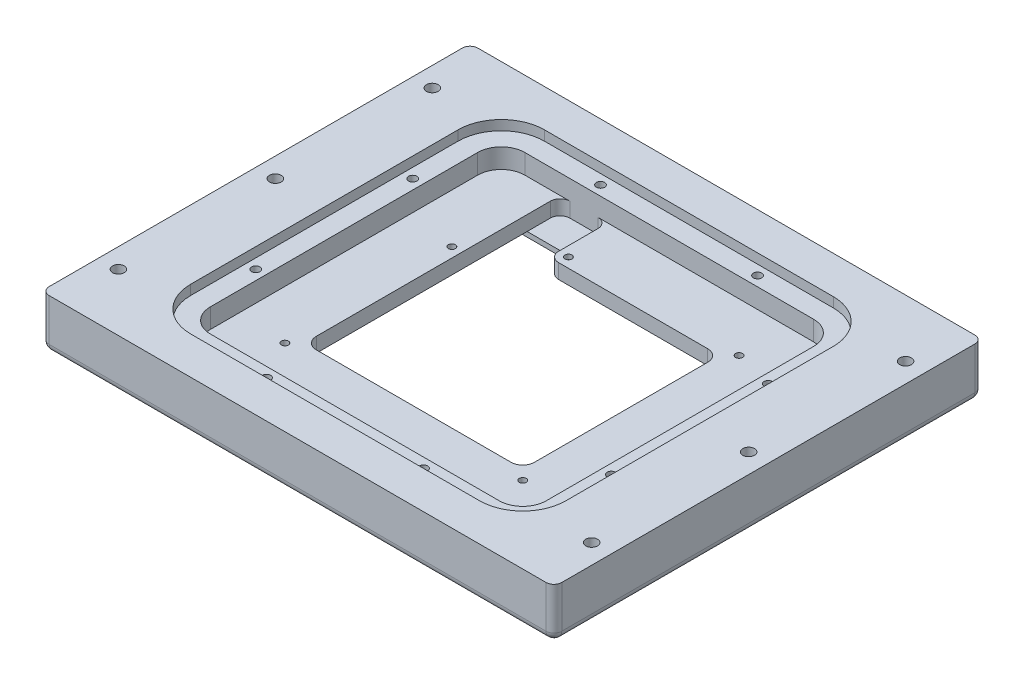
SolidWorks part; units mm, degrees
material "PE High Density"
ref_plane "Front Plane" through (0, 0, 0) normal (0, 0, 1) x (1, 0, 0)
ref_plane "Top Plane" through (0, 0, 0) normal (0, 1, 0) x (1, 0, 0)
ref_plane "Right Plane" through (0, 0, 0) normal (1, 0, 0) x (0, 0, -1)
sketch "Sketch2" plane through (0, 0, 0) normal (0, 1, 0) x (1, 0, 0)
  line L0 (-41.656, 22.1996) -> (-19.9136, 22.1996)
  line L1 (41.656, -38.1762) -> (-41.656, -38.1762)
  line L2 (41.656, -38.1762) -> (41.656, 38.1762)
  line L3 (41.656, 38.1762) -> (-41.656, 38.1762)
  line L4 (-41.656, -38.1762) -> (-41.656, 38.1762)
  line L5 (41.656, -38.1762) -> (-41.656, 38.1762) construction
  line L6 (41.656, 38.1762) -> (-41.656, -38.1762) construction
  line L7 (-19.9136, 22.1996) -> (-19.9136, 38.1762)
  line L8 (73.406, -69.9262) -> (-73.406, -69.9262)
  line L9 (-73.406, -69.9262) -> (-73.406, 69.9262)
  line L10 (73.406, 69.9262) -> (-73.406, 69.9262)
  line L11 (73.406, -69.9262) -> (73.406, 69.9262)
  point P0 (0, 0)
  point P13 (-38.481, -35.0012)
  point P14 (38.481, -35.0012)
  point P15 (38.481, 35.0012)
  point P16 (-16.7386, 35.0012)
  point P17 (-38.481, 19.0246)
  dimension "D1" = 83.312
  dimension "D2" = 76.3524
  dimension "D3" = 21.7424
  dimension "D4" = 15.9766
  dimension "D6" = 3.175
  dimension "D7" = 3.175
  dimension "D8" = 57.2008
  dimension "D9" = 80.137
  dimension "D10" = 24.9174
  dimension "D11" = 73.1774
  dimension "D5" = 31.75
extrude "Boss-Extrude1" add sketch "Sketch2" along normal blind 15.875 contours L8 L11 L10 L9 L1 L4 L3 L2 | L0 L7 L3 L4
sketch "Sketch4" plane through (0, 0, 0) normal (0, 1, 0) x (1, 0, 0)
  line L0 (41.656, -38.1762) -> (41.656, 38.1762) construction
  line L1 (41.656, 38.1762) -> (-19.9136, 38.1762) construction
  line L2 (41.656, -38.1762) -> (-41.656, -38.1762) construction
  line L3 (-41.656, -38.1762) -> (-41.656, 22.1996) construction
  line L4 (-41.656, 22.1996) -> (-19.9136, 22.1996) construction
  line L5 (41.656, -38.1762) -> (41.656, 38.1762)
  line L6 (41.656, 38.1762) -> (-19.9136, 38.1762)
  line L7 (41.656, -38.1762) -> (-41.656, -38.1762)
  line L8 (-41.656, -38.1762) -> (-41.656, 22.1996)
  line L9 (-41.656, 22.1996) -> (-19.9136, 22.1996)
  line L10 (-19.9136, 22.1996) -> (-19.9136, 38.1762) construction
  line L11 (-19.9136, 22.1996) -> (-19.9136, 38.1762)
  line L12 (35.306, 31.8262) -> (-13.5636, 31.8262)
  line L13 (-13.5636, 15.8496) -> (-13.5636, 31.8262)
  line L14 (-35.306, 15.8496) -> (-13.5636, 15.8496)
  line L15 (-35.306, -31.8262) -> (-35.306, 15.8496)
  line L16 (35.306, -31.8262) -> (-35.306, -31.8262)
  line L17 (35.306, -31.8262) -> (35.306, 31.8262)
  dimension "D1" = 6.35
extrude "Boss-Extrude2" add sketch "Sketch4" along normal blind 9.525
sketch "Sketch5" plane through (0, 0, 0) normal (0, -1, 0) x (1, 0, 0)
  line L5 (46.736, -50.8762) -> (-46.736, -50.8762)
  line L6 (54.356, -43.2562) -> (54.356, 43.2562)
  line L7 (46.736, 50.8762) -> (-46.736, 50.8762)
  line L8 (-54.356, -43.2562) -> (-54.356, 43.2562)
  line L9 (54.356, -50.8762) -> (-54.356, 50.8762) construction
  line L10 (54.356, 50.8762) -> (-54.356, -50.8762) construction
  arc A0 (46.736, -50.8762) -> (54.356, -43.2562) centre (46.736, -43.2562) ccw
  arc A1 (-46.736, -50.8762) -> (-54.356, -43.2562) centre (-46.736, -43.2562) cw
  arc A2 (54.356, 43.2562) -> (46.736, 50.8762) centre (46.736, 43.2562) ccw
  arc A3 (-46.736, 50.8762) -> (-54.356, 43.2562) centre (-46.736, 43.2562) ccw
  point P0 (0, 0)
  dimension "D3" = 7.62
  dimension "D1" = 108.712
  dimension "D2" = 101.7524
extrude "Cut-Extrude2" cut sketch "Sketch5" against normal blind 3.175
hole_wizard "M2.5x0.45 Tapped Hole1" positions "Sketch6" profile "Sketch7" tap size "M2.5x0.45" standard "ANSI Metric"
sketch "Sketch6" plane through (0, 3.175, 0) normal (0, -1, 0) x (-1, 0, 0)
  point P0 (38.481, -35.0012)
  point P3 (-38.481, -35.0012)
  point P6 (38.481, 19.0246)
  point P9 (16.7386, 35.0012)
  point P12 (-38.481, 35.0012)
sketch "Sketch7" plane through (-38.481, 3.175, 35.0012) normal (1, 0, 0) x (0, 0, -1)
  line L0 (0, 0) -> (0, 6.9659)
  line L1 (0, 6.9659) -> (1.025, 6.35)
  line L2 (1.025, 6.35) -> (1.025, 0)
  line L5 (1.025, 0) -> (0, 0)
  line L10 (0, 6.9659) -> (-1.025, 6.35) construction
  line L11 (0, -6.35) -> (0, 107.95) construction
  dimension "Tap Drill Dia." = 2.05
  dimension "Tap Drill Depth" = 6.35
  dimension "Drill Angle" = 118
cosmetic thread "Hole Thread1" parameters "D1"=5.08, "D2"=2.5
cosmetic thread "Hole Thread2" parameters "D1"=5.08, "D2"=2.5
cosmetic thread "Hole Thread3" parameters "D1"=5.08, "D2"=2.5
cosmetic thread "Hole Thread4" parameters "D1"=5.08, "D2"=2.5
cosmetic thread "Hole Thread5" parameters "D1"=5.08, "D2"=2.5
sketch "Sketch10" plane through (0, 15.875, 0) normal (0, 1, 0) x (1, 0, 0)
  line L4 (54.356, -43.2562) -> (54.356, 43.2562)
  line L5 (-46.736, -50.8762) -> (46.736, -50.8762)
  line L6 (-54.356, 43.2562) -> (-54.356, -43.2562)
  line L7 (46.736, 50.8762) -> (-46.736, 50.8762)
  line L8 (54.356, -43.2562) -> (54.356, 43.2562)
  line L9 (-46.736, -50.8762) -> (46.736, -50.8762)
  line L10 (-54.356, 43.2562) -> (-54.356, -43.2562)
  line L11 (46.736, 50.8762) -> (-46.736, 50.8762)
  arc A4 (54.356, 43.2562) -> (46.736, 50.8762) centre (46.736, 43.2562) ccw
  arc A5 (46.736, -50.8762) -> (54.356, -43.2562) centre (46.736, -43.2562) ccw
  arc A6 (-54.356, -43.2562) -> (-46.736, -50.8762) centre (-46.736, -43.2562) ccw
  arc A7 (-46.736, 50.8762) -> (-54.356, 43.2562) centre (-46.736, 43.2562) ccw
  arc A8 (54.356, 43.2562) -> (46.736, 50.8762) centre (46.736, 43.2562) ccw
  arc A9 (46.736, -50.8762) -> (54.356, -43.2562) centre (46.736, -43.2562) ccw
  arc A10 (-54.356, -43.2562) -> (-46.736, -50.8762) centre (-46.736, -43.2562) ccw
  arc A11 (-46.736, 50.8762) -> (-54.356, 43.2562) centre (-46.736, 43.2562) ccw
  dimension "D1" = 0
extrude "Cut-Extrude3" cut sketch "Sketch10" against normal up to surface (6.35 mm away) up to face at (-38.481, 9.525, 33.9762)
sketch "Sketch11" plane through (0, 3.175, 0) normal (0, -1, 0) x (1, 0, 0)
  line L8 (43.688, 40.2082) -> (-43.688, 40.2082)
  line L9 (-43.688, 40.2082) -> (-43.688, -40.2082)
  line L10 (-43.688, -40.2082) -> (43.688, -40.2082)
  line L11 (43.688, -40.2082) -> (43.688, 40.2082)
  line L12 (40.513, 40.2082) -> (-40.513, 40.2082)
  line L13 (-43.688, 37.0332) -> (-43.688, -37.0332)
  line L14 (-40.513, -40.2082) -> (40.513, -40.2082)
  line L15 (43.688, -37.0332) -> (43.688, 37.0332)
  arc A0 (40.513, -40.2082) -> (43.688, -37.0332) centre (40.513, -37.0332) ccw
  arc A1 (-43.688, -37.0332) -> (-40.513, -40.2082) centre (-40.513, -37.0332) ccw
  arc A2 (40.513, 40.2082) -> (43.688, 37.0332) centre (40.513, 37.0332) cw
  arc A3 (-40.513, 40.2082) -> (-43.688, 37.0332) centre (-40.513, 37.0332) ccw
  dimension "D2" = 3.175
  dimension "D1" = 2.032
extrude "Cut-Extrude4" cut sketch "Sketch11" against normal blind 1.6
sketch "Sketch12" plane through (0, 4.775, 0) normal (0, -1, 0) x (1, 0, 0)
  line L0 (-35.306, 31.8262) -> (-35.306, -15.8496) construction
  line L1 (35.306, 31.8262) -> (-35.306, 31.8262)
  line L2 (35.306, 31.8262) -> (35.306, -31.8262)
  line L3 (35.306, -31.8262) -> (-35.306, -31.8262)
  line L4 (-35.306, 31.8262) -> (-35.306, -31.8262)
  line L5 (-13.5636, -31.8262) -> (35.306, -31.8262) construction
extrude "Cut-Extrude5" cut sketch "Sketch12" against normal through all
fillet "Fillet1" radius 3.81 4 edges at (35.306, 7.15, -31.8262) (-35.306, 7.15, -31.8262) (35.306, 7.15, 31.8262) (-35.306, 7.15, 31.8262)
sketch "Sketch13" plane through (0, 0, 0) normal (0, -1, 0) x (1, 0, 0)
  line L4 (54.356, -43.2562) -> (54.356, 43.2562)
  line L5 (46.736, 50.8762) -> (-46.736, 50.8762)
  line L6 (-54.356, 43.2562) -> (-54.356, -43.2562)
  line L7 (-46.736, -50.8762) -> (46.736, -50.8762)
  line L8 (54.356, -43.2562) -> (54.356, 43.2562)
  line L9 (46.736, 50.8762) -> (-46.736, 50.8762)
  line L10 (-54.356, 43.2562) -> (-54.356, -43.2562)
  line L11 (-46.736, -50.8762) -> (46.736, -50.8762)
  line L12 (73.406, 69.9262) -> (-73.406, 69.9262)
  line L13 (-73.406, 69.9262) -> (-73.406, -69.9262)
  line L14 (-73.406, -69.9262) -> (73.406, -69.9262)
  line L15 (73.406, -69.9262) -> (73.406, 69.9262)
  line L16 (73.406, 69.9262) -> (-73.406, 69.9262)
  line L17 (-73.406, 69.9262) -> (-73.406, -69.9262)
  line L18 (-73.406, -69.9262) -> (73.406, -69.9262)
  line L19 (73.406, -69.9262) -> (73.406, 69.9262)
  arc A4 (46.736, -50.8762) -> (54.356, -43.2562) centre (46.736, -43.2562) ccw
  arc A5 (54.356, 43.2562) -> (46.736, 50.8762) centre (46.736, 43.2562) ccw
  arc A6 (-46.736, 50.8762) -> (-54.356, 43.2562) centre (-46.736, 43.2562) ccw
  arc A7 (-54.356, -43.2562) -> (-46.736, -50.8762) centre (-46.736, -43.2562) ccw
  arc A8 (46.736, -50.8762) -> (54.356, -43.2562) centre (46.736, -43.2562) ccw
  arc A9 (54.356, 43.2562) -> (46.736, 50.8762) centre (46.736, 43.2562) ccw
  arc A10 (-46.736, 50.8762) -> (-54.356, 43.2562) centre (-46.736, 43.2562) ccw
  arc A11 (-54.356, -43.2562) -> (-46.736, -50.8762) centre (-46.736, -43.2562) ccw
  dimension "D1" = 0
  dimension "D2" = 0
extrude "Cut-Extrude6" cut sketch "Sketch13" against normal blind 1.5875
fillet "Fillet2" [suppressed] radius 1.5875
sketch "Sketch14" plane through (0, 9.525, 0) normal (0, 1, 0) x (1, 0, 0)
  line L1 (-35.306, 28.0162) -> (-19.9136, 28.0162)
  line L2 (-35.306, 28.0162) -> (-35.306, 50.8762)
  line L3 (-35.306, 50.8762) -> (-19.9136, 50.8762)
  line L4 (-19.9136, 28.0162) -> (-19.9136, 50.8762)
  line L6 (46.736, 50.8762) -> (-46.736, 50.8762) construction
  circle A0 centre (-16.7386, 35.0012) radius 1.025 construction
  dimension "D1" = 3.175
extrude "Cut-Extrude7" cut sketch "Sketch14" against normal up to surface (4.75 mm away) up to face at (0, 4.775, 0)
fillet "Fillet3" radius 3.175 3 edges at (-19.9136, 7.15, -50.8762) (-35.306, 7.15, -50.8762) (-19.9136, 7.15, -31.8262)
sketch "Sketch15" plane through (0, 15.875, 0) normal (0, 1, 0) x (1, 0, 0)
  line L0 (54.356, -43.2562) -> (54.356, 43.2562) construction
  line L1 (-46.736, -50.8762) -> (46.736, -50.8762) construction
  line L2 (-54.356, 43.2562) -> (-54.356, -43.2562) construction
  line L3 (46.736, 50.8762) -> (-46.736, 50.8762) construction
  line L4 (54.356, -43.2562) -> (54.356, 43.2562)
  line L5 (-46.736, -50.8762) -> (46.736, -50.8762)
  line L6 (-54.356, 43.2562) -> (-54.356, -43.2562)
  line L7 (46.736, 50.8762) -> (-46.736, 50.8762)
  line L8 (60.706, -43.2562) -> (60.706, 43.2562)
  line L9 (46.736, 57.2262) -> (-46.736, 57.2262)
  line L10 (-60.706, 43.2562) -> (-60.706, -43.2562)
  line L11 (-46.736, -57.2262) -> (46.736, -57.2262)
  line L16 (-73.406, -69.9262) -> (73.406, -69.9262)
  line L17 (73.406, -69.9262) -> (73.406, 69.9262)
  line L18 (73.406, 69.9262) -> (-73.406, 69.9262)
  line L19 (-73.406, 69.9262) -> (-73.406, -69.9262)
  line L20 (-73.406, -69.9262) -> (73.406, -69.9262)
  line L21 (73.406, -69.9262) -> (73.406, 69.9262)
  line L22 (73.406, 69.9262) -> (-73.406, 69.9262)
  line L23 (-73.406, 69.9262) -> (-73.406, -69.9262)
  arc A0 (46.736, -50.8762) -> (54.356, -43.2562) centre (46.736, -43.2562) ccw construction
  arc A1 (-54.356, -43.2562) -> (-46.736, -50.8762) centre (-46.736, -43.2562) ccw construction
  arc A2 (54.356, 43.2562) -> (46.736, 50.8762) centre (46.736, 43.2562) ccw construction
  arc A3 (-46.736, 50.8762) -> (-54.356, 43.2562) centre (-46.736, 43.2562) ccw construction
  arc A4 (46.736, -50.8762) -> (54.356, -43.2562) centre (46.736, -43.2562) ccw
  arc A5 (-54.356, -43.2562) -> (-46.736, -50.8762) centre (-46.736, -43.2562) ccw
  arc A6 (54.356, 43.2562) -> (46.736, 50.8762) centre (46.736, 43.2562) ccw
  arc A7 (-46.736, 50.8762) -> (-54.356, 43.2562) centre (-46.736, 43.2562) ccw
  arc A8 (60.706, 43.2562) -> (46.736, 57.2262) centre (46.736, 43.2562) ccw
  arc A9 (-46.736, 57.2262) -> (-60.706, 43.2562) centre (-46.736, 43.2562) ccw
  arc A10 (-60.706, -43.2562) -> (-46.736, -57.2262) centre (-46.736, -43.2562) ccw
  arc A11 (46.736, -57.2262) -> (60.706, -43.2562) centre (46.736, -43.2562) ccw
  line M29 (-73.406, -69.9262) -> (73.406, -69.9262)
  line M30 (73.406, -69.9262) -> (73.406, 69.9262)
  line M31 (73.406, 69.9262) -> (-73.406, 69.9262)
  line M32 (-73.406, 69.9262) -> (-73.406, -69.9262)
  dimension "D1" = 6.35
  dimension "D2" = 0
extrude "Boss-Extrude3" add sketch "Sketch15" along normal blind 3.175 contours A11 L11 A10 L10 A9 L9 A8 L8 M32 M29 M30 M31
hole_wizard "#6-32 Tapped Hole1" positions "Sketch16" profile "Sketch18" tap size "#6-32" standard "ANSI Inch"
sketch "Sketch16" plane through (0, 15.875, 0) normal (0, 1, 0) x (1, 0, 0)
  line L28 (57.531, -43.2562) -> (57.531, 43.2562)
  line L29 (-46.736, -54.0512) -> (46.736, -54.0512)
  line L30 (-57.531, 43.2562) -> (-57.531, -43.2562)
  line L31 (46.736, 54.0512) -> (-46.736, 54.0512)
  line L32 (57.531, -43.2562) -> (57.531, 43.2562) construction
  line L33 (-46.736, -54.0512) -> (46.736, -54.0512) construction
  line L34 (-57.531, 43.2562) -> (-57.531, -43.2562) construction
  line L35 (46.736, 54.0512) -> (-46.736, 54.0512) construction
  arc A24 (57.531, 43.2562) -> (46.736, 54.0512) centre (46.736, 43.2562) ccw
  arc A25 (46.736, -54.0512) -> (57.531, -43.2562) centre (46.736, -43.2562) ccw
  arc A26 (-57.531, -43.2562) -> (-46.736, -54.0512) centre (-46.736, -43.2562) ccw
  arc A27 (-46.736, 54.0512) -> (-57.531, 43.2562) centre (-46.736, 43.2562) ccw
  arc A28 (57.531, 43.2562) -> (46.736, 54.0512) centre (46.736, 43.2562) ccw construction
  arc A29 (46.736, -54.0512) -> (57.531, -43.2562) centre (46.736, -43.2562) ccw construction
  arc A30 (-57.531, -43.2562) -> (-46.736, -54.0512) centre (-46.736, -43.2562) ccw construction
  arc A31 (-46.736, 54.0512) -> (-57.531, 43.2562) centre (-46.736, 43.2562) ccw construction
  point P141 (-25.4, 54.0512)
  point P143 (-57.531, 25.4)
  point P145 (-57.531, -25.4)
  point P147 (-25.4, -54.0512)
  dimension "D2" = 25.4
  dimension "D3" = 25.4
  dimension "D4" = 25.4
  dimension "D1" = 3.175
cosmetic thread "Hole Thread6" parameters "D1"=14.224, "D2"=3.5052
cosmetic thread "Hole Thread7" parameters "D1"=14.224, "D2"=3.5052
cosmetic thread "Hole Thread8" parameters "D1"=14.224, "D2"=3.5052
cosmetic thread "Hole Thread9" parameters "D1"=14.224, "D2"=3.5052
sketch "Sketch18" plane through (-25.4, 15.875, 54.0512) normal (1, 0, 0) x (0, 0, 1)
  line L0 (0, 0) -> (0, 10.3377)
  line L1 (0, 10.3377) -> (1.3525, 9.525)
  line L2 (1.3525, 9.525) -> (1.3525, 0)
  line L5 (1.3525, 0) -> (0, 0)
  line L10 (0, 10.3377) -> (-1.3526, 9.525) construction
  line L11 (0, -6.35) -> (0, 107.95) construction
  dimension "Tap Drill Dia." = 2.7051
  dimension "Tap Drill Depth" = 9.525
  dimension "Drill Angle" = 118
mirror "Mirror1" about plane through (0, 0, 0) normal (1, 0, 0) of "#6-32 Tapped Hole1"
cosmetic thread "Hole Thread10" parameters "D1"=14.224, "D2"=3.5052
cosmetic thread "Hole Thread11" parameters "D1"=14.224, "D2"=3.5052
cosmetic thread "Hole Thread12" parameters "D1"=14.224, "D2"=3.5052
cosmetic thread "Hole Thread13" parameters "D1"=14.224, "D2"=3.5052
sketch "Sketch19" plane through (0, 4.775, 0) normal (0, -1, 0) x (1, 0, 0)
  circle A0 centre (38.481, 35.0012) radius 2.7813
  circle A1 centre (38.481, -35.0012) radius 2.7813
  circle A2 centre (-38.481, 35.0012) radius 2.7813
  circle A3 centre (-38.481, -19.0246) radius 2.7813
  circle A4 centre (-16.7386, -35.0012) radius 2.7813
  point P0 (38.481, 35.0012)
  dimension "D1" = 5.5626
  dimension "D2" = 5.5626
  dimension "D3" = 5.5626
  dimension "D4" = 5.5626
  dimension "D5" = 5.5626
extrude "Cut-Extrude8" cut sketch "Sketch19" against normal blind 3.175
hole_wizard "#4-40 Tapped Hole1" positions "Sketch20" profile "Sketch21" tap size "#4-40" standard "ANSI Inch"
sketch "Sketch20" plane through (0, 9.525, 0) normal (0, 1, 0) x (1, 0, 0)
  point P0 (-38.481, 19.0246)
  point P3 (-16.7386, 35.0012)
  point P6 (38.481, 35.0012)
  point P9 (38.481, -35.0012)
  point P12 (-38.481, -35.0012)
sketch "Sketch21" plane through (-38.481, 9.525, -19.0246) normal (1, 0, 0) x (0, 0, 1)
  line L0 (0, 0) -> (0, 8.2992)
  line L1 (0, 8.2992) -> (1.1303, 7.62)
  line L2 (1.1303, 7.62) -> (1.1303, 0)
  line L5 (1.1303, 0) -> (0, 0)
  line L10 (0, 8.2992) -> (-1.1303, 7.62) construction
  line L11 (0, -6.35) -> (0, 107.95) construction
  dimension "Tap Drill Dia." = 2.2606
  dimension "Tap Drill Depth" = 7.62
  dimension "Drill Angle" = 118
cosmetic thread "Hole Thread14" parameters "D1"=5.588, "D2"=2.8448
cosmetic thread "Hole Thread15" parameters "D1"=5.588, "D2"=2.8448
cosmetic thread "Hole Thread16" parameters "D1"=5.588, "D2"=2.8448
cosmetic thread "Hole Thread17" parameters "D1"=5.588, "D2"=2.8448
cosmetic thread "Hole Thread18" parameters "D1"=5.588, "D2"=2.8448
sketch "Sketch22" plane through (0, 1.5875, 0) normal (0, -1, 0) x (1, 0, 0)
  line L0 (73.406, -69.9262) -> (73.406, 69.9262) construction
  line L1 (73.406, 69.9262) -> (-73.406, 69.9262)
  line L2 (73.406, 69.9262) -> (73.406, -69.9262)
  line L3 (73.406, -69.9262) -> (-73.406, -69.9262)
  line L4 (-73.406, 69.9262) -> (-73.406, -69.9262)
  line L5 (73.406, 69.9262) -> (-73.406, 69.9262) construction
  line L6 (-73.406, 69.9262) -> (-73.406, -69.9262) construction
  line L7 (-73.406, -69.9262) -> (73.406, -69.9262) construction
extrude "Cut-Extrude9" cut sketch "Sketch22" against normal blind 1.524
sketch "Sketch23" plane through (0, 3.175, 0) normal (0, -1, 0) x (1, 0, 0)
  line L9 (46.736, 44.2722) -> (-46.736, 44.2722)
  line L10 (46.736, 44.2722) -> (46.736, 50.8762)
  line L11 (46.736, 50.8762) -> (-46.736, 50.8762)
  line L12 (-46.736, 44.2722) -> (-46.736, 50.8762)
  line L13 (54.356, 43.2562) -> (47.752, 43.2562)
  line L14 (54.356, 43.2562) -> (54.356, -43.2562)
  line L15 (54.356, -43.2562) -> (47.752, -43.2562)
  line L16 (47.752, 43.2562) -> (47.752, -43.2562)
  line L17 (46.736, -50.8762) -> (-46.736, -50.8762)
  line L18 (46.736, -50.8762) -> (46.736, -44.2722)
  line L19 (46.736, -44.2722) -> (-46.736, -44.2722)
  line L20 (-46.736, -50.8762) -> (-46.736, -44.2722)
  line L21 (-54.356, 43.2562) -> (-47.752, 43.2562)
  line L22 (-54.356, 43.2562) -> (-54.356, -43.2562)
  line L23 (-54.356, -43.2562) -> (-47.752, -43.2562)
  line L24 (-47.752, 43.2562) -> (-47.752, -43.2562)
  arc A0 (54.356, -43.2562) -> (46.736, -50.8762) centre (46.736, -43.2562) cw
  arc A1 (47.752, -43.2562) -> (46.736, -44.2722) centre (46.736, -43.2562) cw
  arc A2 (-46.736, -50.8762) -> (-54.356, -43.2562) centre (-46.736, -43.2562) cw
  arc A3 (-46.736, -44.2722) -> (-47.752, -43.2562) centre (-46.736, -43.2562) cw
  arc A4 (-54.356, 43.2562) -> (-46.736, 50.8762) centre (-46.736, 43.2562) cw
  arc A5 (-47.752, 43.2562) -> (-46.736, 44.2722) centre (-46.736, 43.2562) cw
  arc A6 (46.736, 50.8762) -> (54.356, 43.2562) centre (46.736, 43.2562) cw
  arc A7 (46.736, 44.2722) -> (47.752, 43.167) centre (46.6914, 43.2116) cw
  arc M26 (46.736, -50.8762) -> (54.356, -43.2562) centre (46.736, -43.2562) ccw
  line M27 (54.356, -43.2562) -> (54.356, 43.2562)
  arc M28 (54.356, 43.2562) -> (46.736, 50.8762) centre (46.736, 43.2562) ccw
  line M29 (46.736, 50.8762) -> (-46.736, 50.8762)
  arc M30 (-46.736, 50.8762) -> (-54.356, 43.2562) centre (-46.736, 43.2562) ccw
  line M31 (-54.356, 43.2562) -> (-54.356, -43.2562)
  arc M32 (-54.356, -43.2562) -> (-46.736, -50.8762) centre (-46.736, -43.2562) ccw
  line M33 (-46.736, -50.8762) -> (46.736, -50.8762)
  dimension "D1" = 6.604
extrude "Cut-Extrude10" cut sketch "Sketch23" against normal blind 0.6801 contours L21 A5 L12 M30 | L12 L9 L10 M29 | L24 L21 L23 M31 | L10 A7 L13 M28 | L13 A7 L16 L15 M27 | L15 A1 L18 M26 | L20 L18 L19 M33 | L20 A3 L23 M32
sketch "Sketch24" plane through (0, 19.05, 0) normal (0, 1, 0) x (1, 0, 0)
  line L0 (-73.406, -69.9262) -> (73.406, -69.9262) construction
  line L1 (73.406, -69.9262) -> (73.406, 69.9262) construction
  line L2 (-73.406, 69.9262) -> (-73.406, -69.9262) construction
  line L3 (73.406, 69.9262) -> (-73.406, 69.9262) construction
  point P0 (67.056, -69.9262)
  point P1 (73.406, 63.5762)
  point P4 (67.056, 69.9262)
  point P5 (-67.056, -69.9262)
  point P6 (73.406, -63.5762)
  point P7 (-73.406, 63.5762)
  point P10 (-73.406, -63.5762)
  point P17 (-67.056, 69.9262)
  point P18 (-67.056, -63.5762)
  point P21 (-67.056, 63.5762)
  point P22 (67.056, -63.5762)
  point P23 (67.056, 63.5762)
  dimension "D1" = 6.35
  dimension "D2" = 6.35
  dimension "D3" = 6.35
  dimension "D4" = 6.35
  dimension "D5" = 6.35
  dimension "D6" = 6.35
  dimension "D7" = 6.35
  dimension "D8" = 6.35
hole_wizard "1/4-20 Tapped Hole1" [suppressed] positions "Sketch27" profile "Sketch28" tap size "1/4-20" standard "ANSI Inch"
sketch "Sketch27" plane through (0, 19.05, 0) normal (0, 1, 0) x (1, 0, 0)
  point P0 (67.056, -63.5762)
  point P9 (67.056, 63.5762)
  point P24 (41.656, -63.5762)
  point P26 (67.056, -38.1762)
  point P28 (67.056, 38.1762)
  point P30 (41.656, 63.5762)
  point P39 (16.256, -63.5762)
  point P41 (67.056, -12.7762)
  point P43 (67.056, 12.7762)
  point P45 (16.256, 63.5762)
  dimension "D1" = 25.4
  dimension "D2" = 25.4
  dimension "D3" = 25.4
  dimension "D4" = 25.4
  dimension "D5" = 25.4
  dimension "D6" = 25.4
sketch "Sketch28" plane through (67.056, 19.05, 63.5762) normal (1, 0, 0) x (0, 0, 1)
  line L0 (0, 0) -> (0, 18.0438)
  line L1 (0, 18.0438) -> (2.5527, 16.51)
  line L2 (2.5527, 16.51) -> (2.5527, 0)
  line L5 (2.5527, 0) -> (0, 0)
  line L10 (0, 18.0438) -> (-2.5527, 16.51) construction
  line L11 (0, -6.35) -> (0, 107.95) construction
  dimension "Tap Drill Dia." = 5.1054
  dimension "Tap Drill Depth" = 16.51
  dimension "Drill Angle" = 118
cosmetic thread "Hole Thread19" [suppressed] parameters "D1"=12.7, "D2"=6.35
cosmetic thread "Hole Thread20" [suppressed] parameters "D1"=12.7, "D2"=6.35
cosmetic thread "Hole Thread21" [suppressed] parameters "D1"=12.7, "D2"=6.35
cosmetic thread "Hole Thread22" [suppressed] parameters "D1"=12.7, "D2"=6.35
cosmetic thread "Hole Thread23" [suppressed] parameters "D1"=12.7, "D2"=6.35
cosmetic thread "Hole Thread24" [suppressed] parameters "D1"=12.7, "D2"=6.35
cosmetic thread "Hole Thread25" [suppressed] parameters "D1"=12.7, "D2"=6.35
cosmetic thread "Hole Thread26" [suppressed] parameters "D1"=12.7, "D2"=6.35
cosmetic thread "Hole Thread27" [suppressed] parameters "D1"=12.7, "D2"=6.35
cosmetic thread "Hole Thread28" [suppressed] parameters "D1"=12.7, "D2"=6.35
mirror "Mirror2" [suppressed] about plane through (0, 0, 0) normal (1, 0, 0)
cosmetic thread "Hole Thread29" [suppressed] parameters "D1"=12.7, "D2"=6.35
cosmetic thread "Hole Thread30" [suppressed] parameters "D1"=12.7, "D2"=6.35
cosmetic thread "Hole Thread31" [suppressed] parameters "D1"=12.7, "D2"=6.35
cosmetic thread "Hole Thread32" [suppressed] parameters "D1"=12.7, "D2"=6.35
cosmetic thread "Hole Thread33" [suppressed] parameters "D1"=12.7, "D2"=6.35
cosmetic thread "Hole Thread34" [suppressed] parameters "D1"=12.7, "D2"=6.35
cosmetic thread "Hole Thread35" [suppressed] parameters "D1"=12.7, "D2"=6.35
cosmetic thread "Hole Thread36" [suppressed] parameters "D1"=12.7, "D2"=6.35
cosmetic thread "Hole Thread37" [suppressed] parameters "D1"=12.7, "D2"=6.35
cosmetic thread "Hole Thread38" [suppressed] parameters "D1"=12.7, "D2"=6.35
sketch "Sketch29" plane through (0, 19.05, 0) normal (0, 1, 0) x (1, 0, 0)
  line L0 (-82.931, 79.4512) -> (-82.931, -79.4512)
  line L1 (-82.931, -79.4512) -> (82.931, -79.4512)
  line L2 (82.931, -79.4512) -> (82.931, 79.4512)
  line L3 (82.931, 79.4512) -> (-82.931, 79.4512)
  line L4 (-73.406, 69.9262) -> (-73.406, -69.9262)
  line L5 (-73.406, -69.9262) -> (73.406, -69.9262)
  line L6 (73.406, -69.9262) -> (73.406, 69.9262)
  line L7 (73.406, 69.9262) -> (-73.406, 69.9262)
  line L8 (-73.406, 69.9262) -> (-73.406, -69.9262)
  line L9 (-73.406, -69.9262) -> (73.406, -69.9262)
  line L10 (73.406, -69.9262) -> (73.406, 69.9262)
  line L11 (73.406, 69.9262) -> (-73.406, 69.9262)
  dimension "D1" = 0
  dimension "D2" = 9.525
extrude "Boss-Extrude4" add sketch "Sketch29" against normal up to surface (15.9385 mm away) up to face at (0, 3.1115, 0)
sketch "Sketch30" plane through (0, 3.1115, 0) normal (0, -1, 0) x (1, 0, 0)
  line L0 (46.736, 50.8762) -> (-46.736, 50.8762) construction
  line L1 (46.736, 50.8762) -> (-46.736, 50.8762)
  line L2 (-54.356, 43.2562) -> (-54.356, -43.2562) construction
  line L3 (-54.356, 43.2562) -> (-54.356, -43.2562)
  line L4 (-82.931, -79.4512) -> (82.931, -79.4512)
  line L5 (82.931, -79.4512) -> (82.931, 79.4512)
  line L6 (82.931, 79.4512) -> (-82.931, 79.4512)
  line L7 (-82.931, 79.4512) -> (-82.931, -79.4512)
  line L8 (-82.931, -79.4512) -> (82.931, -79.4512)
  line L9 (82.931, -79.4512) -> (82.931, 79.4512)
  line L10 (82.931, 79.4512) -> (-82.931, 79.4512)
  line L11 (-82.931, 79.4512) -> (-82.931, -79.4512)
  line L14 (-46.736, -50.8762) -> (46.736, -50.8762)
  line L15 (-54.356, 43.2562) -> (-54.356, -43.2562)
  line L16 (46.736, 50.8762) -> (-46.736, 50.8762)
  line L17 (54.356, -43.2562) -> (54.356, 43.2562)
  line L18 (-46.736, -50.8762) -> (46.736, -50.8762)
  line L19 (-54.356, 43.2562) -> (-54.356, -43.2562)
  line L20 (46.736, 50.8762) -> (-46.736, 50.8762)
  line L21 (54.356, -43.2562) -> (54.356, 43.2562)
  arc A0 (-46.736, 50.8762) -> (-54.356, 43.2562) centre (-46.736, 43.2562) ccw construction
  arc A1 (-46.736, 50.8762) -> (-54.356, 43.2562) centre (-46.736, 43.2562) ccw
  arc A4 (-54.356, -43.2562) -> (-46.736, -50.8762) centre (-46.736, -43.2562) ccw
  arc A5 (-46.736, 50.8762) -> (-54.356, 43.2562) centre (-46.736, 43.2562) ccw
  arc A6 (54.356, 43.2562) -> (46.736, 50.8762) centre (46.736, 43.2562) ccw
  arc A7 (46.736, -50.8762) -> (54.356, -43.2562) centre (46.736, -43.2562) ccw
  arc A8 (-54.356, -43.2562) -> (-46.736, -50.8762) centre (-46.736, -43.2562) ccw
  arc A9 (-46.736, 50.8762) -> (-54.356, 43.2562) centre (-46.736, 43.2562) ccw
  arc A10 (54.356, 43.2562) -> (46.736, 50.8762) centre (46.736, 43.2562) ccw
  arc A11 (46.736, -50.8762) -> (54.356, -43.2562) centre (46.736, -43.2562) ccw
  dimension "D1" = 0
  dimension "D2" = 0
extrude "Boss-Extrude5" add sketch "Sketch30" along normal blind 0.2718
sketch "Sketch31" [suppressed] plane through (0, 19.05, 0) normal (0, 1, 0) x (1, 0, 0)
  circle A0 centre (16.256, -63.5762) radius 2.5527 construction
  circle A1 centre (67.056, -12.7762) radius 2.5527 construction
  circle A2 centre (67.056, 12.7762) radius 2.5527 construction
  circle A3 centre (16.256, 63.5762) radius 2.5527 construction
  circle A4 centre (-16.256, 63.5762) radius 2.5527 construction
  circle A5 centre (-67.056, 12.7762) radius 2.5527 construction
  circle A6 centre (-67.056, -12.7762) radius 2.5527 construction
  circle A7 centre (-16.256, -63.5762) radius 2.5527 construction
  circle A8 centre (16.256, -63.5762) radius 2.5527
  circle A9 centre (67.056, -12.7762) radius 2.5527
  circle A10 centre (67.056, 12.7762) radius 2.5527
  circle A11 centre (16.256, 63.5762) radius 2.5527
  circle A12 centre (-16.256, 63.5762) radius 2.5527
  circle A13 centre (-67.056, 12.7762) radius 2.5527
  circle A14 centre (-67.056, -12.7762) radius 2.5527
  circle A15 centre (-16.256, -63.5762) radius 2.5527
extrude "Boss-Extrude6" [suppressed] add sketch "Sketch31" against normal up to surface (16.2103 mm away)
sketch "Sketch32" [suppressed] plane through (0, 19.05, 0) normal (0, 1, 0) x (1, 0, 0)
  line L0 (82.931, -79.4512) -> (82.931, 79.4512) construction
  line L1 (-82.931, -79.4512) -> (82.931, -79.4512) construction
  line L2 (-82.931, 79.4512) -> (-82.931, -79.4512) construction
  line L3 (82.931, 79.4512) -> (-82.931, 79.4512) construction
  line L4 (82.931, -79.4512) -> (82.931, 79.4512)
  line L5 (-82.931, -79.4512) -> (82.931, -79.4512)
  line L6 (-82.931, 79.4512) -> (-82.931, -79.4512)
  line L7 (82.931, 79.4512) -> (-82.931, 79.4512)
  line L9 (76.581, -73.1012) -> (-76.581, -73.1012)
  line L10 (76.581, -73.1012) -> (76.581, 73.1012)
  line L11 (76.581, 73.1012) -> (-76.581, 73.1012)
  line L12 (-76.581, -73.1012) -> (-76.581, 73.1012)
  line L13 (76.581, -73.1012) -> (-76.581, 73.1012) construction
  line L14 (76.581, 73.1012) -> (-76.581, -73.1012) construction
  circle A0 centre (-67.056, 63.5762) radius 2.5527 construction
  point P3 (0, 0)
  dimension "D1" = 9.525
  dimension "D2" = 9.525
extrude "Cut-Extrude11" [suppressed] cut sketch "Sketch32" against normal through all
sketch "Sketch33" [suppressed] plane through (0, 19.05, 0) normal (0, 1, 0) x (1, 0, 0)
  line L0 (76.581, 73.1012) -> (-76.581, 73.1012) construction
  line L1 (83.185, -73.1012) -> (-83.185, -73.1012)
  line L2 (83.185, -73.1012) -> (83.185, 73.1012)
  line L3 (83.185, 73.1012) -> (-83.185, 73.1012)
  line L4 (-83.185, -73.1012) -> (-83.185, 73.1012)
  line L5 (83.185, -73.1012) -> (-83.185, 73.1012) construction
  line L6 (83.185, 73.1012) -> (-83.185, -73.1012) construction
  line L7 (-76.581, 73.1012) -> (-76.581, -73.1012) construction
  line L12 (-46.736, -57.2262) -> (46.736, -57.2262)
  line L13 (-60.706, 43.2562) -> (-60.706, -43.2562)
  line L14 (46.736, 57.2262) -> (-46.736, 57.2262)
  line L15 (60.706, -43.2562) -> (60.706, 43.2562)
  line L16 (-46.736, -57.2262) -> (46.736, -57.2262)
  line L17 (-60.706, 43.2562) -> (-60.706, -43.2562)
  line L18 (46.736, 57.2262) -> (-46.736, 57.2262)
  line L19 (60.706, -43.2562) -> (60.706, 43.2562)
  arc A0 (-46.736, 57.2262) -> (-60.706, 43.2562) centre (-46.736, 43.2562) ccw construction
  arc A1 (-46.736, 57.2262) -> (-60.706, 43.2562) centre (-46.736, 43.2562) ccw
  arc A4 (46.736, -57.2262) -> (60.706, -43.2562) centre (46.736, -43.2562) ccw
  arc A5 (-60.706, -43.2562) -> (-46.736, -57.2262) centre (-46.736, -43.2562) ccw
  arc A6 (-46.736, 57.2262) -> (-60.706, 43.2562) centre (-46.736, 43.2562) ccw
  arc A7 (60.706, 43.2562) -> (46.736, 57.2262) centre (46.736, 43.2562) ccw
  arc A8 (46.736, -57.2262) -> (60.706, -43.2562) centre (46.736, -43.2562) ccw
  arc A9 (-60.706, -43.2562) -> (-46.736, -57.2262) centre (-46.736, -43.2562) ccw
  arc A10 (-46.736, 57.2262) -> (-60.706, 43.2562) centre (-46.736, 43.2562) ccw
  arc A11 (60.706, 43.2562) -> (46.736, 57.2262) centre (46.736, 43.2562) ccw
  point P0 (0, 0)
  arc M13 (60.706, -43.2562) -> (46.736, -57.2262) centre (46.736, -43.2562) cw
  line M14 (46.736, -57.2262) -> (-46.736, -57.2262)
  arc M15 (-46.736, -57.2262) -> (-60.706, -43.2562) centre (-46.736, -43.2562) cw
  line M16 (-60.706, -43.2562) -> (-60.706, 43.2562)
  arc M17 (-60.706, 43.2562) -> (-46.736, 57.2262) centre (-46.736, 43.2562) cw
  line M18 (-46.736, 57.2262) -> (46.736, 57.2262)
  arc M19 (46.736, 57.2262) -> (60.706, 43.2562) centre (46.736, 43.2562) cw
  line M20 (60.706, 43.2562) -> (60.706, -43.2562)
  circle M21 centre (41.656, 63.5762) radius 2.5527
  circle M22 centre (67.056, 38.1762) radius 2.5527
  circle M23 centre (67.056, -38.1762) radius 2.5527
  circle M24 centre (41.656, -63.5762) radius 2.5527
  circle M25 centre (67.056, 63.5762) radius 2.5527
  circle M26 centre (67.056, -63.5762) radius 2.5527
  circle M27 centre (-41.656, 63.5762) radius 2.5527
  circle M28 centre (-67.056, 38.1762) radius 2.5527
  circle M29 centre (-67.056, -38.1762) radius 2.5527
  circle M30 centre (-41.656, -63.5762) radius 2.5527
  circle M31 centre (-67.056, 63.5762) radius 2.5527
  circle M32 centre (-67.056, -63.5762) radius 2.5527
  line M33 (76.581, 73.1012) -> (-76.581, 73.1012)
  line M34 (-76.581, 73.1012) -> (-76.581, -73.1012)
  line M35 (-76.581, -73.1012) -> (76.581, -73.1012)
  line M36 (76.581, -73.1012) -> (76.581, 73.1012)
  dimension "D1" = 6.604
  dimension "D2" = 0
extrude "Boss-Extrude7" [suppressed] add sketch "Sketch33" against normal up to surface (16.2103 mm away) contours M36 M33 M34 M35 M22 M24 M26 M28 M30 M32 M31 M29 M27 M25 M23 M21 M20 M13 M14 M15 M16 M17 M18 M19 | L4 L1 L3 M34 | L2 L3 L1 M36
sketch "Sketch34" plane through (0, 19.05, 0) normal (0, 1, 0) x (1, 0, 0)
  line L0 (82.931, -79.4512) -> (82.931, 79.4512) construction
  line L1 (-82.931, -79.4512) -> (82.931, -79.4512)
  line L2 (-82.931, -79.4512) -> (-82.931, -69.3649)
  line L3 (-82.931, -69.3649) -> (82.931, -69.3649)
  line L4 (82.931, -79.4512) -> (82.931, -69.3649)
  line L5 (-82.931, 79.4512) -> (-82.931, -79.4512) construction
  line L6 (82.931, 79.4512) -> (-82.931, 79.4512)
  line L7 (82.931, 79.4512) -> (82.931, 69.3649)
  line L8 (82.931, 69.3649) -> (-82.931, 69.3649)
  line L9 (-82.931, 79.4512) -> (-82.931, 69.3649)
  dimension "D1" = 10.0863
  dimension "D2" = 10.0863
extrude "Cut-Extrude12" cut sketch "Sketch34" against normal through all
fillet "Fillet4" radius 2.54 8 edges at (-82.931, 2.8397, 0) (82.931, 2.8397, 0) (0, 2.8397, 69.3649) (0, 2.8397, -69.3649) (-82.931, 10.9449, -69.3649) (82.931, 10.9449, -69.3649) (-82.931, 10.9449, 69.3649) (82.931, 10.9449, 69.3649)
hole_wizard "CBORE for #6 Socket Head Cap Screw1" positions "Sketch35" profile "Sketch36" counterbore size "#6" standard "ANSI Inch" end condition through all
sketch "Sketch35" plane through (0, 2.8397, 0) normal (0, -1, 0) x (-1, 0, 0)
  line L0 (82.931, 66.8249) -> (82.931, -66.8249) construction
  point P0 (76.581, -50.8)
  point P2 (76.581, 0)
  point P4 (76.581, 50.8)
  point P8 (0, 0)
  dimension "D1" = 6.35
  dimension "D2" = 50.8
  dimension "D3" = 50.8
sketch "Sketch36" plane through (-76.581, 2.8397, 50.8) normal (1, 0, 0) x (0, 0, -1)
  line L0 (0, 0) -> (0, 16.2103)
  line L1 (0, 16.2103) -> (1.8986, 16.2103)
  line L3 (1.8986, 16.2103) -> (1.8987, 3.5052)
  line L4 (1.8987, 3.5052) -> (3.5725, 3.5052)
  line L5 (3.5725, 3.5052) -> (3.5725, 0)
  line L7 (3.5725, 0) -> (0, 0)
  line L11 (0, -6.35) -> (0, 107.95) construction
  dimension "Thru Hole Dia." = 3.7973
  dimension "Thru Hole Depth" = 16.2103
  dimension "C'Bore Dia." = 7.145
  dimension "C'Bore Depth" = 3.5052
mirror "Mirror3" about plane through (0, 0, 0) normal (1, 0, 0) of "CBORE for #6 Socket Head Cap Screw1"
equation "\"D3@Sketch16\"=\"D2@Sketch16\""
equation "\"D4@Sketch16\"=\"D2@Sketch16\""
